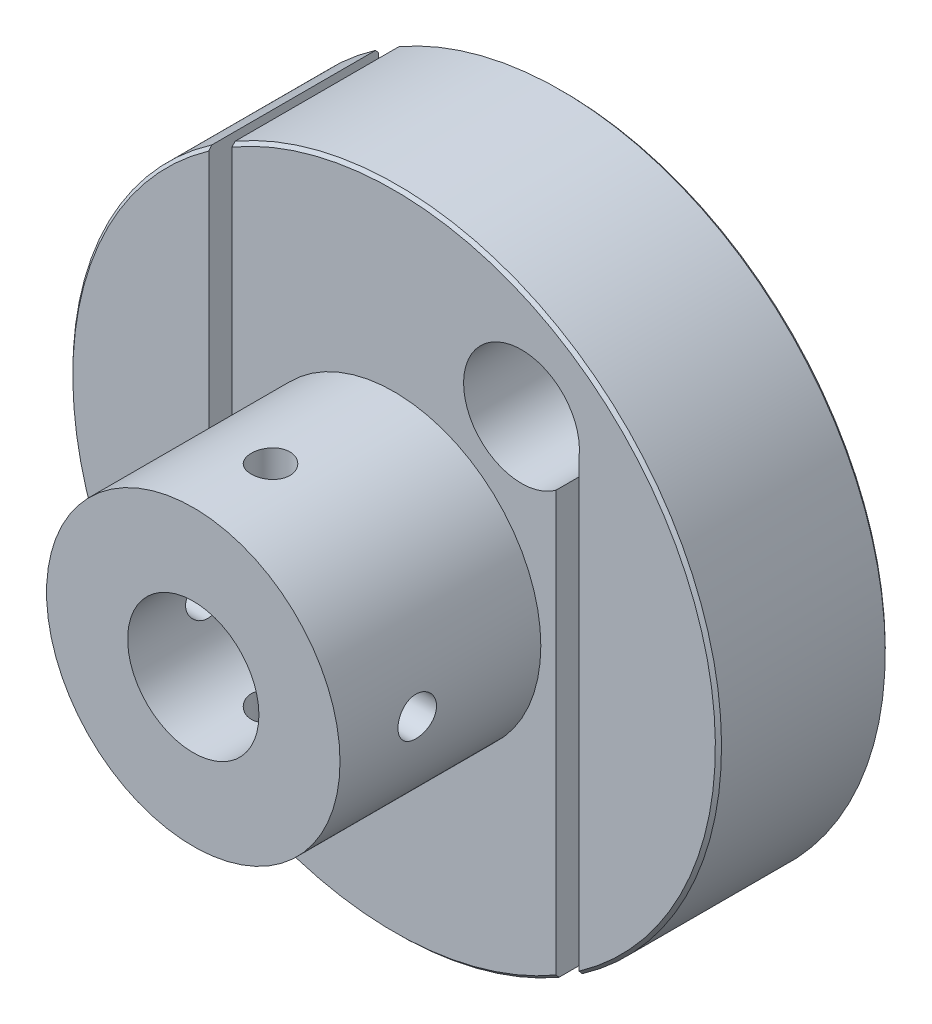
SolidWorks part; units mm, degrees
ref_plane "Plan de face" through (0, 0, 0) normal (0, 0, 1) x (1, 0, 0)
ref_plane "Plan de dessus" through (0, 0, 0) normal (0, 1, 0) x (1, 0, 0)
ref_plane "Plan de droite" through (0, 0, 0) normal (1, 0, 0) x (0, 0, -1)
sketch "Esquisse1" plane through (0, 0, 0) normal (0, 0, 1) x (1, 0, 0)
  circle A0 centre (0, 0) radius 21
  dimension "D1" = 42
extrude "Boss.-Extru.1" add sketch "Esquisse1" along normal blind 11
sketch "Esquisse2" plane through (0, 0, 11) normal (0, 0, 1) x (1, 0, 0)
  circle A0 centre (0, 0) radius 9.5
  dimension "D1" = 19
extrude "Boss.-Extru.2" add sketch "Esquisse2" along normal blind 13
sketch "Esquisse3" plane through (0, 0, 24) normal (0, 0, 1) x (1, 0, 0)
  circle A0 centre (0, 0) radius 4.25
  dimension "D1" = 8.5
extrude "Enlèv. mat.-Extru.1" cut sketch "Esquisse3" against normal through all
sketch "Esquisse4" plane through (0, 0, 11) normal (0, 0, 1) x (1, 0, 0)
  line L0 (0, 0) -> (0, 21.1146) construction
  line L1 (0, 0) -> (0, -23.7008) construction
  line L2 (-12, 19.627) -> (-12, -23.7008) construction
  line L3 (12, 19.627) -> (12, -23.7008) construction
  circle A0 centre (8.25, 12.227) radius 3.75
  circle A2 centre (-8.25, -12.227) radius 3.75
  circle A7 centre (0, 0) radius 11
  circle A8 centre (0, 0) radius 11 construction
  dimension "D1" = 1.5
  dimension "D2" = 7.5
  dimension "D3" = 12
extrude "Enlèv. mat.-Extru.2" cut sketch "Esquisse4" against normal through all
sketch "Esquisse5" plane through (0, 0, 11) normal (0, 0, 1) x (1, 0, 0)
  line L0 (-11.9947, -12.0277) -> (-11.9947, 19.9703)
  line L1 (-10.4947, -12.0277) -> (-10.4947, 19.9703)
  line L2 (-11.9947, 19.9703) -> (-10.4947, 19.9703)
  line L3 (-11.9947, -12.0277) -> (-10.4947, -12.0277)
  line L4 (11.9789, 12.6241) -> (11.9789, -19.0205)
  line L5 (10.4789, 12.6241) -> (10.4789, -19.0205)
  line L6 (10.4789, 10.7687) -> (10.4789, -17.2622) construction
  line L7 (11.9789, 10.7687) -> (11.9789, -17.2622) construction
  line L8 (11.9789, 12.6241) -> (10.4789, 12.6241)
  line L9 (10.4789, -19.0205) -> (11.9789, -19.0205)
  circle A2 centre (-8.25, -12.227) radius 3.75 construction
  circle A3 centre (8.25, 12.227) radius 3.75 construction
  dimension "D1" = 1.5
  dimension "D2" = 1.5
extrude "Enlèv. mat.-Extru.3" cut sketch "Esquisse5" against normal through all
ref_plane "Plan1" through (0, 10, 0) normal (0, 1, 0) x (1, 0, 0)
hole_wizard "Trou pour taraudage pour trou taraudé M31" positions "Esquisse7" profile "Esquisse6" hole size "M3" standard "DIN" end condition through all
sketch "Esquisse7" plane through (0, 10, 0) normal (0, 1, 0) x (1, 0, 0)
  line L0 (-9.5, -24) -> (9.5, -24) construction
  point P0 (0, -19)
  dimension "D1" = 5
sketch "Esquisse6" plane through (0, 10, 19) normal (1, 0, 0) x (0, 0, 1)
  line L0 (0, 0) -> (0, 31)
  line L1 (0, 31) -> (1.25, 31)
  line L2 (1.25, 31) -> (1.25, 0)
  line L5 (1.25, 0) -> (0, 0)
  line L11 (0, -6.35) -> (0, 107.95) construction
  dimension "Diamètre du perçage jusqu'au prochain" = 2.5
  dimension "Profondeur du perçage jusqu'au prochain" = 31
ref_plane "Plan2" through (10, 0, 0) normal (1, 0, 0) x (0, 0, -1)
hole_wizard "Trou pour taraudage pour trou taraudé M32" positions "Esquisse11" profile "Esquisse10" hole size "M3" standard "DIN" end condition through all
sketch "Esquisse11" plane through (10, 0, 0) normal (1, 0, 0) x (0, 0, -1)
  line L0 (-24, 9.5) -> (-24, -9.5) construction
  point P0 (-19, 0)
  dimension "D1" = 5
sketch "Esquisse10" plane through (10, 0, 19) normal (0, 1, 0) x (0, 0, -1)
  line L0 (0, 0) -> (0, 31)
  line L1 (0, 31) -> (1.25, 31)
  line L2 (1.25, 31) -> (1.25, 0)
  line L5 (1.25, 0) -> (0, 0)
  line L11 (0, -6.35) -> (0, 107.95) construction
  dimension "Diamètre du perçage jusqu'au prochain" = 2.5
  dimension "Profondeur du perçage jusqu'au prochain" = 31
chamfer "Chanfrein1" distance 0.2 angle 45 5 edges at (-17.7342, -11.2471, 11) (-17.7342, -11.2471, 0) (17.7345, 11.2467, 11) (17.7345, 11.2467, 0) (4.25, 0, 0)
